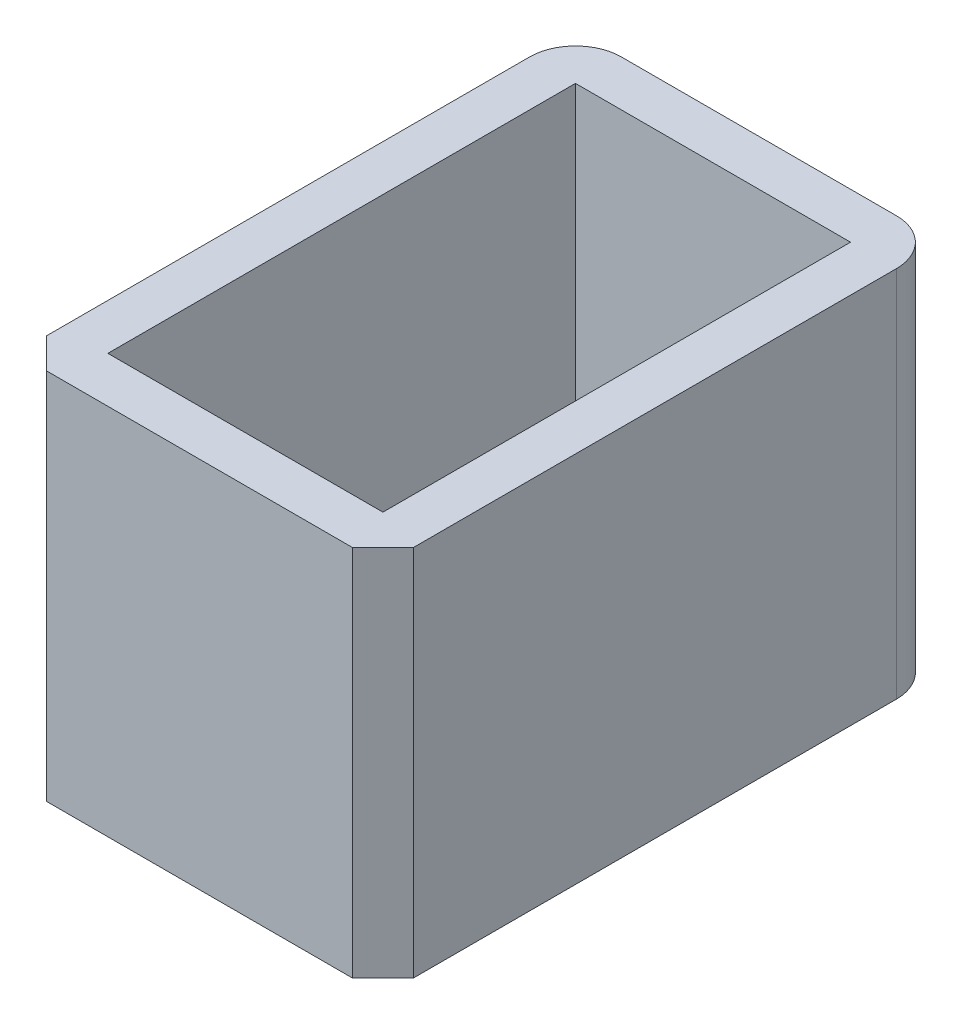
SolidWorks part; units mm, degrees
ref_plane "Front Plane" through (0, 0, 0) normal (0, 0, 1) x (1, 0, 0)
ref_plane "Top Plane" through (0, 0, 0) normal (0, 1, 0) x (1, 0, 0)
ref_plane "Right Plane" through (0, 0, 0) normal (1, 0, 0) x (0, 0, -1)
sketch "Sketch1" plane through (0, 0, 0) normal (0, 1, 0) x (1, 0, 0)
  line L1 (0, 0) -> (24, 0)
  line L2 (0, 0) -> (0, 36.6)
  line L3 (0, 36.6) -> (24, 36.6)
  line L4 (24, 0) -> (24, 36.6)
  dimension "D1" = 24
  dimension "D2" = 36.6
extrude "Boss-Extrude1" add sketch "Sketch1" along normal blind 24.4
sketch "Sketch2" plane through (0, 24.4, 0) normal (0, 1, 0) x (1, 0, 0)
  line L0 (24, 0) -> (24, 36.6) construction
  line L1 (3, 33.6) -> (21, 33.6)
  line L2 (3, 33.6) -> (3, 3)
  line L3 (3, 3) -> (21, 3)
  line L4 (21, 33.6) -> (21, 3)
  line L5 (0, 36.6) -> (0, 0) construction
  line L6 (0, 0) -> (24, 0) construction
  line L7 (24, 36.6) -> (0, 36.6) construction
  dimension "D1" = 3
  dimension "D2" = 3
  dimension "D3" = 3
  dimension "D4" = 3
extrude "Cut-Extrude1" cut sketch "Sketch2" against normal blind 24.4
fillet "Fillet2" radius 3 2 edges at (24, 12.2, -36.6) (0, 12.2, -36.6)
chamfer "Chamfer1" distance 2 angle 45 2 edges at (24, 12.2, 0) (0, 12.2, 0)
